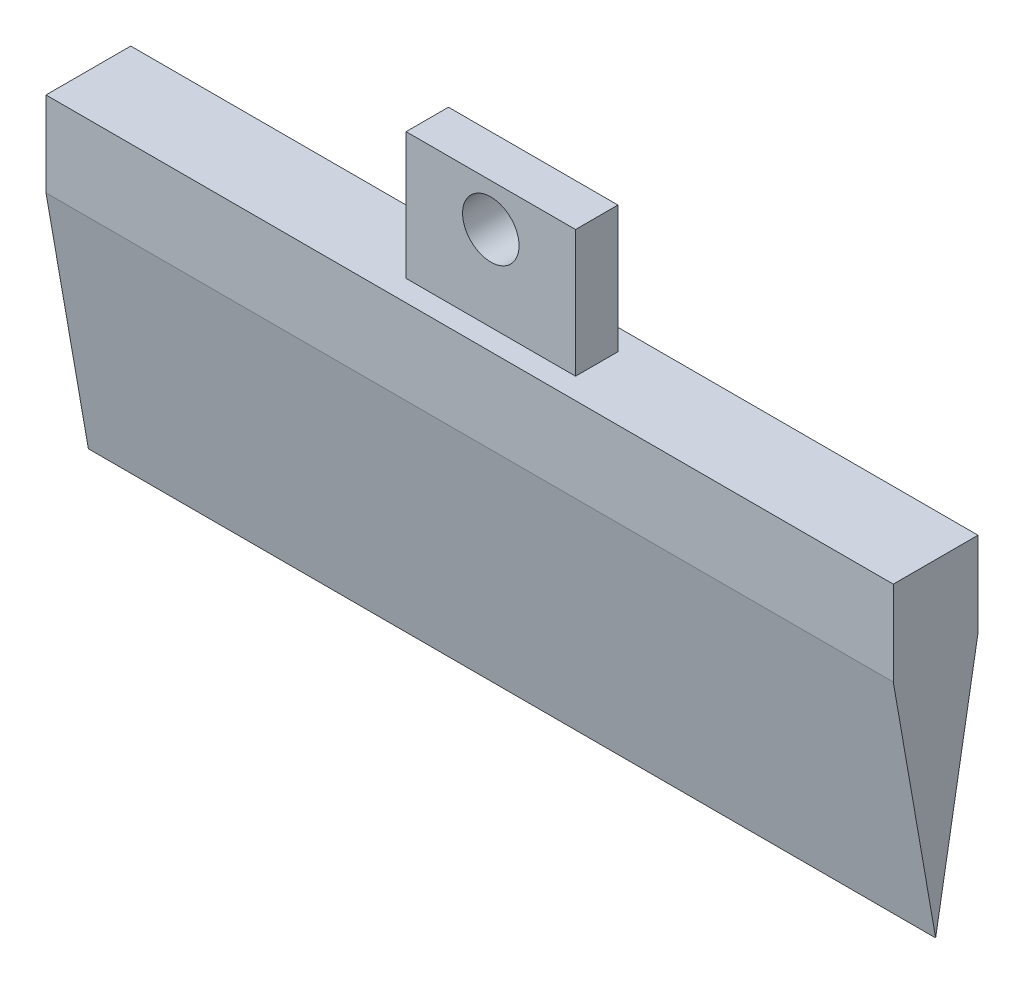
SolidWorks part; units mm, degrees
ref_plane "Front Plane" through (0, 0, 0) normal (0, 0, 1) x (1, 0, 0)
ref_plane "Top Plane" through (0, 0, 0) normal (0, 1, 0) x (1, 0, 0)
ref_plane "Right Plane" through (0, 0, 0) normal (1, 0, 0) x (0, 0, -1)
sketch "Sketch1" plane through (0, 0, 0) normal (1, 0, 0) x (0, 0, -1)
  line L0 (-15, 0) -> (15, 0)
  line L1 (15, 0) -> (15, -30)
  line L2 (15, -30) -> (0, -116)
  line L3 (0, -116) -> (-15, -30)
  line L4 (-15, -30) -> (-15, 0)
  dimension "D1" = 30
  dimension "D2" = 86
  dimension "D3" = 30
extrude "Boss-Extrude1" add sketch "Sketch1" against normal blind 300
sketch "Sketch2" plane through (0, 0, 0) normal (0, 0, 1) x (1, 0, 0)
  line L0 (-300, 0) -> (0, 0) construction
  line L1 (-120, 45) -> (-180, 45)
  line L2 (-120, 45) -> (-120, 0)
  line L3 (-120, 0) -> (-180, 0)
  line L4 (-180, 45) -> (-180, 0)
  line L5 (-300, 0) -> (0, 0) construction
  circle A0 centre (-150, 30) radius 10
  point P8 (-150, 0)
  point P13 (-150, 45)
  dimension "D1" = 20
  dimension "D2" = 60
  dimension "D3" = 30
  dimension "D4" = 45
extrude "Boss-Extrude2" add sketch "Sketch2" along normal mid plane 15
